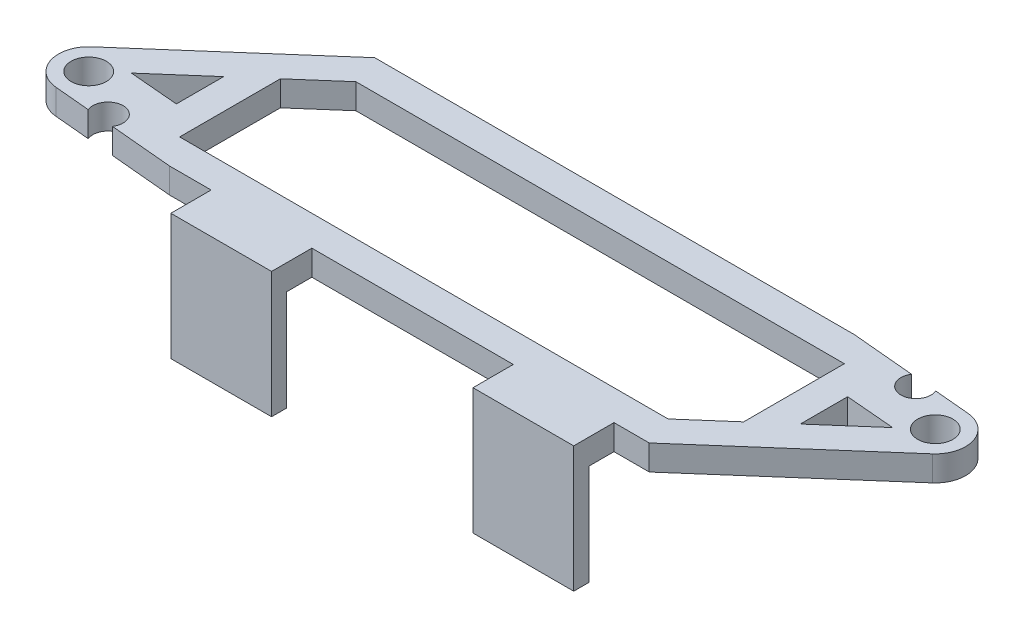
SolidWorks part; units mm, degrees
ref_plane "Front Plane" through (0, 0, 0) normal (0, 0, 1) x (1, 0, 0)
ref_plane "Top Plane" through (0, 0, 0) normal (0, 1, 0) x (1, 0, 0)
ref_plane "Right Plane" through (0, 0, 0) normal (1, 0, 0) x (0, 0, -1)
sketch "Sketch1" plane through (0, 0, 0) normal (0, 1, 0) x (1, 0, 0)
  line L0 (-44.5, 27) -> (52.5, 27)
  line L1 (52.5, 27) -> (52.5, 7)
  line L2 (44.5, 0) -> (-52.5, 0)
  line L3 (-52.5, 0) -> (-52.5, 20)
  line L4 (0, 0) -> (0, 73.3696) construction
  line L5 (-46.7544, 33) -> (48.5, 33)
  line L6 (-46.7544, 33) -> (-76.75, 6.7539)
  line L7 (46.7544, -6) -> (76.75, 20.2461)
  line L8 (46.7544, -6) -> (39.7544, -6)
  line L9 (44.5, 0) -> (52.5, 7)
  line L10 (58.5, 21.65) -> (58.5, 12.25)
  line L11 (58.5, 21.65) -> (68.2835, 20.8106)
  line L12 (58.5, 12.25) -> (68.2835, 20.8106)
  line L13 (48.5, 33) -> (60.9847, 31.8627)
  line L14 (66.2694, 31.3813) -> (73.3433, 30.7368)
  line L15 (-52.5, 20) -> (-44.5, 27)
  line L16 (-58.5, 14.75) -> (-68.2835, 6.1894)
  line L17 (-68.2835, 6.1894) -> (-58.5, 5.35)
  line L18 (-58.5, 5.35) -> (-58.5, 14.75)
  line L19 (-73.3433, -3.7368) -> (-66.2694, -4.3813)
  line L20 (-60.9847, -4.8627) -> (-48.5, -6)
  line L21 (19.7544, -6) -> (19.7544, -14)
  line L22 (19.7544, -14) -> (39.7544, -14)
  line L23 (39.7544, -14) -> (39.7544, -6)
  line L24 (-20.2456, -6) -> (-20.2456, -14)
  line L25 (-20.2456, -14) -> (-40.2456, -14)
  line L26 (-40.2456, -14) -> (-40.2456, -6)
  line L27 (-40.2456, -6) -> (-48.5, -6)
  line L28 (19.7544, -6) -> (-20.2456, -6)
  circle A0 centre (72.799, 24.7616) radius 3.5
  arc A1 (76.75, 20.2461) -> (73.3433, 30.7368) centre (72.799, 24.7616) ccw
  arc A2 (60.9847, 31.8627) -> (66.2694, 31.3813) centre (63.5, 30.2277) ccw
  circle A3 centre (-72.799, 2.2384) radius 3.5
  arc A4 (-76.75, 6.7539) -> (-73.3433, -3.7368) centre (-72.799, 2.2384) ccw
  arc A5 (-66.2694, -4.3813) -> (-60.9847, -4.8627) centre (-63.5, -3.2277) cw
  point P39 (0, 0)
  point P42 (0, 0)
  point P43 (0, 0)
  dimension "D11" = 7
  dimension "D12" = 13
  dimension "D15" = 3
  dimension "D21" = 13
  dimension "D25" = 7
  dimension "D26" = 4
  dimension "D27" = 3
  dimension "D1" = 6
  dimension "D2" = 105
  dimension "D3" = 6
  dimension "D4" = 6
  dimension "D5" = 97
  dimension "D6" = 20
  dimension "D7" = 27
  dimension "D8" = 6
  dimension "D9" = 6
  dimension "D13" = 4
  dimension "D16" = 9.4
  dimension "D17" = 20
  dimension "D18" = 97
  dimension "D19" = 6
  dimension "D20" = 6
  dimension "D22" = 9.4
  dimension "D28" = 1.4
  dimension "D29" = 15
  dimension "D30" = 15
  dimension "D31" = 1.4
  dimension "D32" = 8
  dimension "D33" = 20
  dimension "D34" = 20
  dimension "D35" = 40
  dimension "D36" = 7
extrude "Boss-Extrude1" add sketch "Sketch1" along normal blind 5
sketch "Sketch2" plane through (0, 0, 0) normal (0, -1, 0) x (1, 0, 0)
  line L1 (-40.2456, 14) -> (-20.2456, 14)
  line L2 (-40.2456, 14) -> (-40.2456, 11)
  line L3 (-40.2456, 11) -> (-20.2456, 11)
  line L4 (-20.2456, 14) -> (-20.2456, 11)
  line L5 (39.7544, 14) -> (39.7544, 6) construction
  line L6 (19.7544, 14) -> (39.7544, 14)
  line L7 (19.7544, 14) -> (19.7544, 11)
  line L8 (19.7544, 11) -> (39.7544, 11)
  line L9 (39.7544, 14) -> (39.7544, 11)
  line L10 (-20.2456, 14) -> (-20.2456, 6) construction
  dimension "D1" = 3
extrude "Boss-Extrude2" add sketch "Sketch2" along normal blind 20
